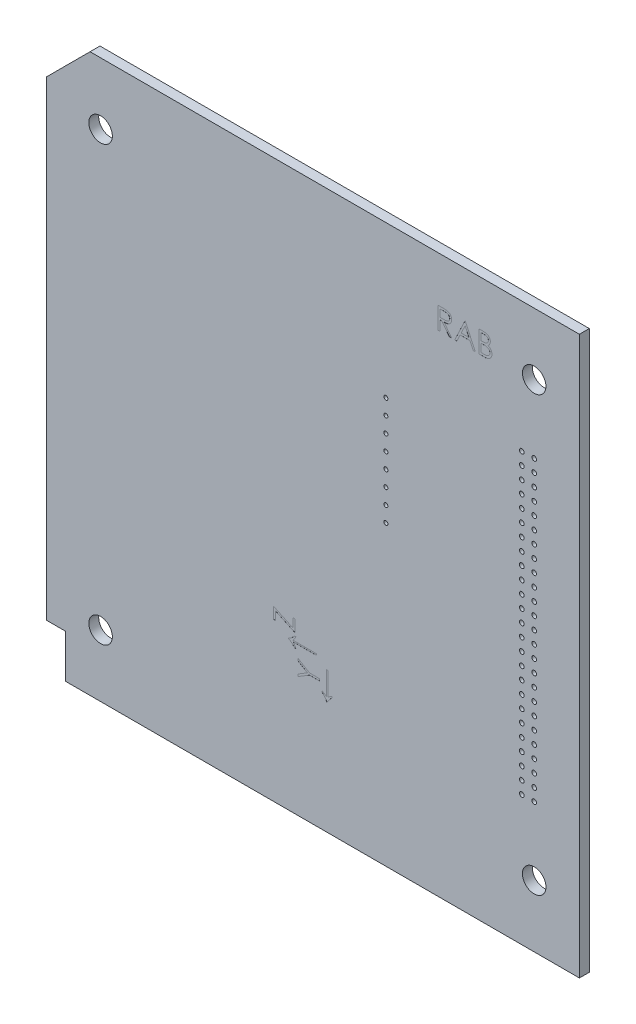
SolidWorks part; units mm, degrees
material "電力回路基板"
ref_plane "正面" through (0, 0, 0) normal (0, 0, 1) x (1, 0, 0)
ref_plane "平面" through (0, 0, 0) normal (0, 1, 0) x (1, 0, 0)
ref_plane "右側面" through (0, 0, 0) normal (1, 0, 0) x (0, 0, -1)
sketch "Sketch1" plane through (0, 0, 0) normal (0, 0, 1) x (1, 0, 0)
  line L0 (0, 0) -> (-86, 0)
  line L1 (0, -90) -> (0, 0)
  line L4 (-86, 0) -> (-86, -90)
  line L14 (0, -90) -> (-86, -90)
  circle A0 centre (-7.3, -10) radius 1.9
  circle A1 centre (-77.3, -10) radius 1.9
  circle A2 centre (-77.3, -80) radius 1.9
  circle A3 centre (-7.3, -80) radius 1.9
  circle A4 centre (-9.3, -69) radius 0.375
  circle A5 centre (-7.3, -69) radius 0.375
  circle A6 centre (-7.3, -67) radius 0.375
  circle A7 centre (-9.3, -67) radius 0.375
  circle A8 centre (-9.3, -65) radius 0.375
  circle A9 centre (-7.3, -65) radius 0.375
  circle A10 centre (-7.3, -63) radius 0.375
  circle A11 centre (-9.3, -63) radius 0.3838
  circle A12 centre (-9.3, -61) radius 0.375
  circle A13 centre (-7.3, -61) radius 0.375
  circle A14 centre (-7.3, -59) radius 0.375
  circle A15 centre (-9.3, -59) radius 0.375
  circle A16 centre (-7.3, -57) radius 0.375
  circle A17 centre (-9.3, -57) radius 0.375
  circle A18 centre (-9.3, -55) radius 0.375
  circle A19 centre (-7.3, -55) radius 0.375
  circle A20 centre (-7.3, -53) radius 0.375
  circle A21 centre (-9.3, -53) radius 0.375
  circle A22 centre (-9.3, -51) radius 0.375
  circle A23 centre (-7.3, -51) radius 0.375
  circle A24 centre (-7.3, -49) radius 0.375
  circle A25 centre (-9.3, -49) radius 0.375
  circle A26 centre (-9.3, -47) radius 0.375
  circle A27 centre (-7.3, -47) radius 0.375
  circle A28 centre (-7.3, -45) radius 0.375
  circle A29 centre (-9.3, -45) radius 0.3842
  circle A30 centre (-9.3, -43) radius 0.375
  circle A31 centre (-7.3, -43) radius 0.3808
  circle A32 centre (-7.3, -41) radius 0.3774
  circle A33 centre (-9.3, -41) radius 0.3774
  circle A34 centre (-9.3, -39) radius 0.375
  circle A35 centre (-7.3, -39) radius 0.375
  circle A36 centre (-7.3, -37) radius 0.375
  circle A37 centre (-9.3, -37) radius 0.3808
  circle A38 centre (-7.3, -35) radius 0.375
  circle A39 centre (-9.3, -35) radius 0.375
  circle A40 centre (-9.3, -33) radius 0.375
  circle A41 centre (-7.3, -33) radius 0.375
  circle A42 centre (-7.3, -31) radius 0.375
  circle A43 centre (-9.3, -31) radius 0.375
  circle A44 centre (-7.3, -29) radius 0.375
  circle A45 centre (-9.3, -29) radius 0.375
  circle A46 centre (-9.3, -27) radius 0.375
  circle A47 centre (-7.3, -27) radius 0.375
  circle A48 centre (-7.3, -25) radius 0.375
  circle A49 centre (-9.3, -25) radius 0.375
  circle A50 centre (-7.3, -23) radius 0.375
  circle A51 centre (-9.3, -23) radius 0.375
  circle A52 centre (-9.3, -21) radius 0.375
  circle A53 centre (-7.3, -21) radius 0.375
  dimension "D5" = 70
  dimension "D6" = 86
  dimension "D3" = 3.8
  dimension "D1" = 86
  dimension "D2" = 90
  dimension "D4" = 70
extrude "Boss-Extrude1" add sketch "Sketch1" along normal blind 1.6
sketch "Sketch2" plane through (0, 0, 0) normal (0, 0, -1) x (-1, 0, 0)
  line L0 (0, -90) -> (0, 0) construction
  line L1 (0, 0) -> (86, 0) construction
  circle A0 centre (31.24, -24.5) radius 0.325
  circle A1 centre (31.24, -27) radius 0.325
  circle A2 centre (31.24, -29.5) radius 0.325
  circle A3 centre (31.24, -32) radius 0.325
  circle A4 centre (31.24, -34.5) radius 0.325
  circle A5 centre (31.24, -37) radius 0.325
  circle A6 centre (31.24, -39.5) radius 0.325
  circle A7 centre (31.24, -42) radius 0.325
  circle A9 centre (31.24, -44.5) radius 0.325 [skipped]
  dimension "D1" = 31.24
  dimension "D2" = 24.5
  dimension "D3" = 9
extrude "Extrude1" cut sketch "Sketch2" against normal through all
sketch "ｽｹｯﾁ1" plane through (0, 0, 1.6) normal (0, 0, 1) x (1, 0, 0)
  text T0 "<r90>Y</r>"
  text T1 "<r90>Z</r>\r\n"
  text T2 "↓"
  text T3 "<r270>↓</r>\r\n"
extrude "ｶｯﾄ - 押し出し1" cut sketch "ｽｹｯﾁ1" against normal blind 0.01
sketch "ｽｹｯﾁ2" plane through (0, 0, 1.6) normal (0, 0, 1) x (1, 0, 0)
  text T0 "RAB"
extrude "ｶｯﾄ - 押し出し2" cut sketch "ｽｹｯﾁ2" against normal blind 0.01
sketch "ｽｹｯﾁ3" plane through (0, 0, 0) normal (0, 0, -1) x (-1, 0, 0)
  line L0 (86, 0) -> (86, -7)
  line L1 (86, -7) -> (79, 0)
  line L2 (79, 0) -> (86, 0)
  line L3 (86, -90) -> (83, -90)
  line L4 (83, -90) -> (83, -83)
  line L5 (83, -83) -> (86, -83)
  line L6 (86, -83) -> (86, -90)
extrude "ｶｯﾄ - 押し出し3" cut sketch "ｽｹｯﾁ3" against normal blind 10
